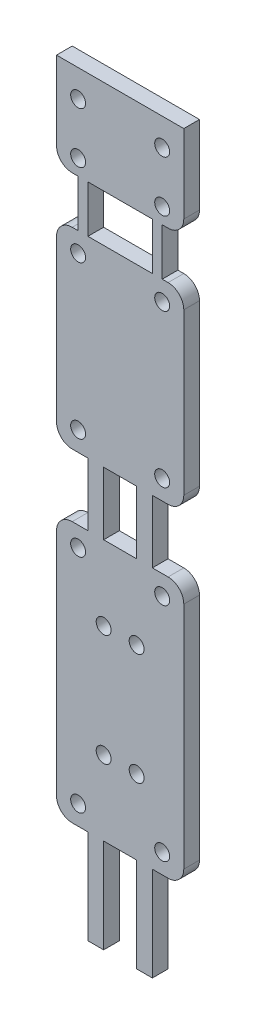
SolidWorks part; units mm, degrees
ref_plane "Front Plane" through (0, 0, 0) normal (0, 0, 1) x (1, 0, 0)
ref_plane "Top Plane" through (0, 0, 0) normal (0, 1, 0) x (1, 0, 0)
ref_plane "Right Plane" through (0, 0, 0) normal (1, 0, 0) x (0, 0, -1)
sketch "Sketch1" plane through (0, 0, 0) normal (0, 0, 1) x (1, 0, 0)
  line L0 (16.2, 1.5) -> (16.2, 14) construction
  line L1 (16.2, 109.64) -> (0, 109.64)
  line L2 (0, 109.64) -> (0, 99.66)
  line L3 (0, 1.5) -> (16.2, 1.5) construction
  line L4 (14.2, 59.21) -> (12.2, 59.21)
  line L5 (0, 14) -> (4, 14) construction
  line L6 (2, 26) -> (4, 26)
  line L7 (2, 91.66) -> (2.75, 91.66)
  line L8 (2, 67.21) -> (4, 67.21)
  line L9 (8.1, 109.64) -> (8.1, 97.66) construction
  line L10 (0, 14) -> (0, 1.5) construction
  line L11 (2, 97.66) -> (2.75, 97.66)
  line L12 (16.2, 28) -> (16.2, 57.21)
  line L13 (16.2, 99.66) -> (16.2, 109.64)
  line L14 (0, 89.66) -> (0, 69.21)
  line L15 (0, 57.21) -> (0, 28)
  line L16 (16.2, 69.21) -> (16.2, 89.66)
  line L17 (6, 14) -> (6, 26)
  line L18 (4, 59.21) -> (4, 67.21)
  line L19 (4, 14) -> (4, 26)
  line L20 (6, 59.21) -> (6, 67.21)
  line L21 (4, 91.66) -> (4, 97.66)
  line L22 (2.75, 97.66) -> (2.75, 91.66)
  line L23 (10.2, 14) -> (10.2, 26)
  line L24 (12.2, 14) -> (12.2, 26)
  line L25 (10.2, 59.21) -> (10.2, 67.21)
  line L26 (12.2, 59.21) -> (12.2, 67.21)
  line L27 (13.45, 91.66) -> (13.45, 97.66)
  line L28 (12.2, 91.66) -> (12.2, 97.66)
  line L29 (4, 97.66) -> (12.2, 97.66)
  line L30 (4, 91.66) -> (12.2, 91.66)
  line L31 (13.45, 91.66) -> (14.2, 91.66)
  line L32 (13.45, 97.66) -> (14.2, 97.66)
  line L33 (6, 67.21) -> (10.2, 67.21)
  line L34 (12.2, 67.21) -> (14.2, 67.21)
  line L35 (10.2, 59.21) -> (6, 59.21)
  line L36 (4, 59.21) -> (2, 59.21)
  line L37 (6, 14) -> (10.2, 14) construction
  line L38 (6, 26) -> (10.2, 26)
  line L39 (12.2, 26) -> (14.2, 26)
  line L40 (12.2, 14) -> (16.2, 14) construction
  line L41 (12.2, 14) -> (10.2, 14)
  line L42 (6, 14) -> (4, 14)
  circle A0 centre (13.45, 56.71) radius 0.95
  circle A1 centre (10.2, 49.71) radius 0.95
  circle A2 centre (13.45, 106.16) radius 0.95
  circle A3 centre (2.75, 99.66) radius 0.95
  circle A4 centre (6, 49.71) radius 0.95
  circle A5 centre (2.75, 28.5) radius 0.95
  circle A6 centre (2.75, 89.16) radius 0.95
  circle A7 centre (2.75, 56.71) radius 0.95
  circle A8 centre (13.45, 89.16) radius 0.95
  circle A9 centre (13.45, 99.66) radius 0.95
  arc A10 (16.2, 28) -> (14.2, 26) centre (14.2, 28) cw
  arc A11 (0, 28) -> (2, 26) centre (2, 28) ccw
  arc A12 (16.2, 57.21) -> (14.2, 59.21) centre (14.2, 57.21) ccw
  arc A13 (0, 57.21) -> (2, 59.21) centre (2, 57.21) cw
  arc A14 (16.2, 69.21) -> (14.2, 67.21) centre (14.2, 69.21) cw
  arc A15 (0, 69.21) -> (2, 67.21) centre (2, 69.21) ccw
  arc A16 (0, 89.66) -> (2, 91.66) centre (2, 89.66) cw
  arc A17 (16.2, 89.66) -> (14.2, 91.66) centre (14.2, 89.66) ccw
  arc A18 (16.2, 99.66) -> (14.2, 97.66) centre (14.2, 99.66) cw
  arc A19 (2, 97.66) -> (0, 99.66) centre (2, 99.66) cw
  circle A28 centre (13.45, 69.71) radius 0.95
  circle A29 centre (6, 35.5) radius 0.95
  circle A32 centre (2.75, 106.16) radius 0.95
  circle A33 centre (10.2, 35.5) radius 0.95
  circle A34 centre (2.75, 69.71) radius 0.95
  circle A35 centre (13.45, 28.5) radius 0.95
  circle A36 centre (2.85, 11.5) radius 0.95 construction
  circle A37 centre (13.35, 11.5) radius 0.95 construction
  circle A38 centre (13.35, 5.5) radius 0.95 construction
  circle A39 centre (2.85, 5.5) radius 0.95 construction
  point P71 (16.2, 26)
  point P74 (0, 26)
  point P91 (16.2, 59.21)
  point P94 (0, 59.21)
  point P97 (16.2, 67.21)
  point P100 (0, 67.21)
  point P103 (0, 91.66)
  point P106 (16.2, 91.66)
  point P109 (16.2, 97.66)
  point P112 (0, 97.66)
  dimension "D1" = 4
  dimension "D45" = 1.9
  dimension "D46" = 2
  dimension "D2" = 4
  dimension "D3" = 2.85
  dimension "D4" = 2.85
  dimension "D5" = 16.2
  dimension "D6" = 6
  dimension "D7" = 6
  dimension "D8" = 2.85
  dimension "D9" = 2.85
  dimension "D10" = 2.5
  dimension "D11" = 12
  dimension "D12" = 33.21
  dimension "D13" = 2.5
  dimension "D14" = 2.5
  dimension "D15" = 2.75
  dimension "D16" = 2.75
  dimension "D17" = 2.5
  dimension "D18" = 2.5
  dimension "D19" = 2.75
  dimension "D20" = 2.75
  dimension "D21" = 9.5
  dimension "D22" = 6
  dimension "D23" = 9.5
  dimension "D24" = 6
  dimension "D25" = 9.5
  dimension "D26" = 9.5
  dimension "D27" = 6
  dimension "D28" = 6
  dimension "D29" = 8
  dimension "D30" = 24.45
  dimension "D31" = 2.5
  dimension "D32" = 2.5
  dimension "D33" = 2.75
  dimension "D34" = 2.75
  dimension "D35" = 6
  dimension "D36" = 2.75
  dimension "D37" = 2
  dimension "D38" = 2.75
  dimension "D39" = 8.5
  dimension "D40" = 11.98
  dimension "D41" = 2.5
  dimension "D42" = 2.5
  dimension "D43" = 2.75
  dimension "D44" = 2.75
extrude "Boss-Extrude1" add sketch "Sketch1" along normal blind 2
sketch "Sketch2" plane through (0, 0, 0) normal (0, 0, -1) x (-1, 0, 0)
  line L0 (-13.45, 97.66) -> (-2.75, 97.66)
  line L1 (-2.75, 97.66) -> (-2.75, 91.66)
  line L2 (-2.75, 91.66) -> (-13.45, 91.66)
  line L3 (-13.45, 91.66) -> (-13.45, 97.66)
  line L4 (-12.2, 67.21) -> (-4, 67.21)
  line L5 (-4, 67.21) -> (-4, 59.21)
  line L6 (-4, 59.21) -> (-12.2, 59.21)
  line L7 (-12.2, 59.21) -> (-12.2, 67.21)
  line L8 (-12.2, 26) -> (-4, 26)
  line L9 (-4, 26) -> (-4, 14)
  line L10 (-4, 14) -> (-12.2, 14)
  line L11 (-12.2, 14) -> (-12.2, 26)
extrude "Cut-Extrude1" [suppressed] cut sketch "Sketch2" against normal up to surface (2 mm away)
equation "\"D12@Sketch1\"= \"HL@parametersSketch@prostheticParameters.SLDPRT\" * 0.266 - 12 - 4 'Middle PIP Length"
equation "\"D30@Sketch1\"= \"HL@parametersSketch@prostheticParameters.SLDPRT\" * 0.17 - 4 - 3'Middle MIP Length"
equation "\"D5@Sketch1\"= \"fingerWidth@parametersSketch@prostheticParameters.SLDPRT\" 'Middle Width"
equation "\"D40@Sketch1\"= \"HL@parametersSketch@prostheticParameters.SLDPRT\" * 0.108 - 3 - 5'Middle DIP Length"
equation "\"D45@Sketch1\"= 1.5 + \"tol1@parametersSketch@prostheticParameters.SLDPRT\""
